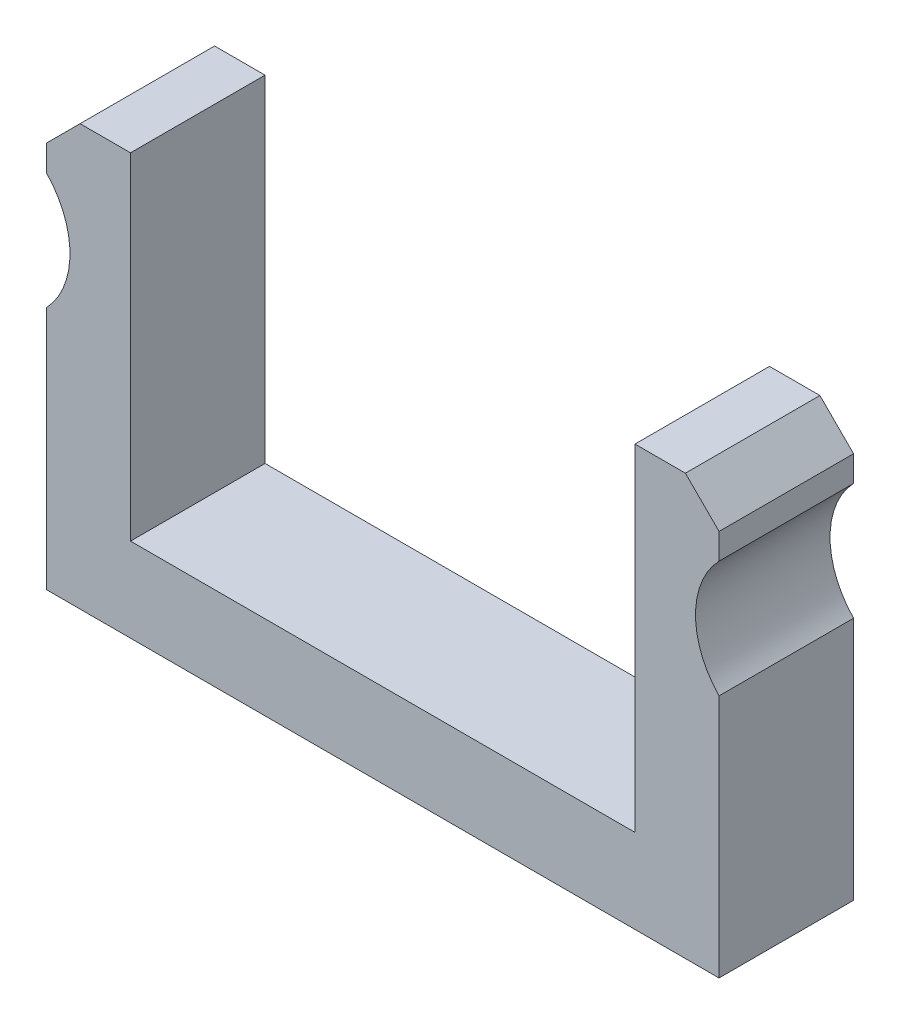
SolidWorks part; units mm, degrees
ref_plane "Front Plane" through (0, 0, 0) normal (0, 0, 1) x (1, 0, 0)
ref_plane "Top Plane" through (0, 0, 0) normal (0, 1, 0) x (1, 0, 0)
ref_plane "Right Plane" through (0, 0, 0) normal (1, 0, 0) x (0, 0, -1)
sketch "Sketch1" plane through (0, 0, 0) normal (0, 0, 1) x (1, 0, 0)
  line L0 (-34.0425, -19.3746) -> (16.7575, -19.3746)
  line L1 (16.7575, -19.3746) -> (16.7575, 12.3754)
  line L2 (16.7575, 12.3754) -> (10.4075, 12.3754)
  line L3 (10.4075, 12.3754) -> (10.4075, -13.0246)
  line L4 (10.4075, -13.0246) -> (-27.6925, -13.0246)
  line L5 (-27.6925, -13.0246) -> (-27.6925, 12.3754)
  line L6 (-34.0425, -19.3746) -> (-34.0425, 12.3754)
  line L7 (-34.0425, 12.3754) -> (-27.6925, 12.3754)
  dimension "D1" = 31.75
  dimension "D2" = 50.8
  dimension "D3" = 6.35
  dimension "D4" = 6.35
  dimension "D5" = 6.35
  dimension "D6" = 31.75
extrude "Boss-Extrude1" add sketch "Sketch1" along normal blind 10.16
sketch "Sketch2" plane through (0, 0, 10.16) normal (0, 0, 1) x (1, 0, 0)
  line L0 (-34.0425, 12.3754) -> (-34.0425, -19.3746) construction
  line L1 (-27.6925, 12.3754) -> (-34.0425, 12.3754) construction
  line L2 (16.7575, -19.3746) -> (16.7575, 12.3754) construction
  line L3 (16.7575, 12.3754) -> (10.4075, 12.3754) construction
  circle A0 centre (-38.6145, 3.4854) radius 6.35
  circle A1 centre (21.3295, 3.4854) radius 6.35
  dimension "D2" = 12.7
  dimension "D4" = 12.7
  dimension "D1" = 4.572
  dimension "D3" = 8.89
  dimension "D5" = 4.572
  dimension "D6" = 8.89
extrude "Cut-Extrude1" cut sketch "Sketch2" against normal blind 25.4
chamfer "Chamfer1" distance 2.54 angle 45 1 edges at (16.7575, 12.3754, 5.08)
chamfer "Chamfer2" distance 2.54 angle 45 1 edges at (-34.0425, 12.3754, 5.08)
